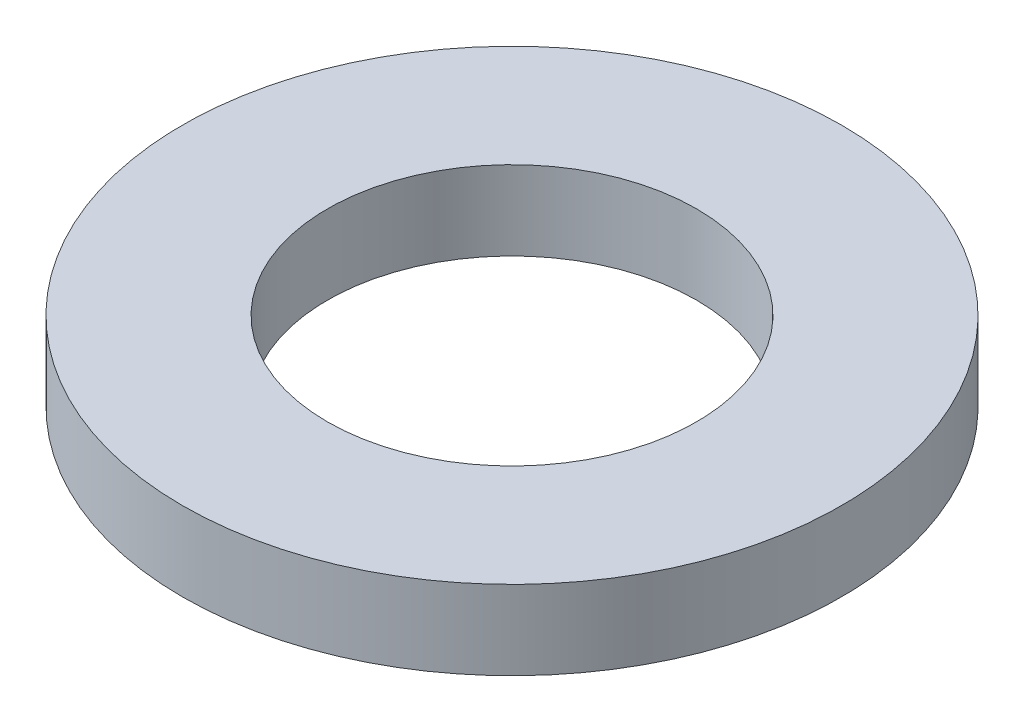
SolidWorks part; units mm, degrees
ref_plane "Ebene vorne" through (0, 0, 0) normal (0, 0, 1) x (1, 0, 0)
ref_plane "Ebene oben" through (0, 0, 0) normal (0, 1, 0) x (1, 0, 0)
ref_plane "Ebene rechts" through (0, 0, 0) normal (1, 0, 0) x (0, 0, -1)
sketch "Skizze1" plane through (0, 0, 0) normal (0, 1, 0) x (1, 0, 0)
  circle A0 centre (0, 0) radius 4.2
  circle A1 centre (0, 0) radius 7.5
  dimension "D1" = 15
  dimension "D2" = 8.4
extrude "Aufsatz-Linear austragen1" add sketch "Skizze1" along normal blind 1.8
